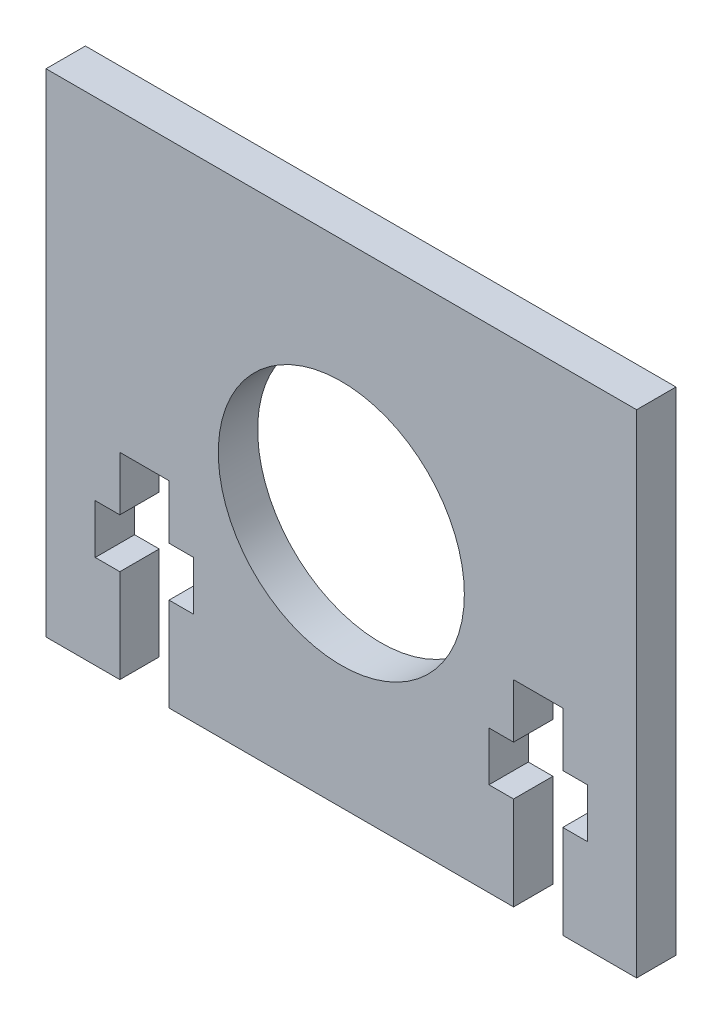
SolidWorks part; units mm, degrees
material "Pine"
ref_plane "Front Plane" through (0, 0, 0) normal (0, 0, 1) x (1, 0, 0)
ref_plane "Top Plane" through (0, 0, 0) normal (0, 1, 0) x (1, 0, 0)
ref_plane "Right Plane" through (0, 0, 0) normal (1, 0, 0) x (0, 0, -1)
sketch "Sketch1" plane through (0, 0, 0) normal (0, 0, 1) x (1, 0, 0)
  line L0 (0, -25) -> (0, 25) construction
  line L1 (30, 25) -> (-30, 25)
  line L2 (30, 25) -> (30, -25)
  line L3 (30, -25) -> (-30, -25)
  line L4 (-30, 25) -> (-30, -25)
  line L5 (30, 25) -> (-30, -25) construction
  line L6 (30, -25) -> (-30, 25) construction
  circle A0 centre (0, 0) radius 12.5
  point P0 (0, 0)
  dimension "D1" = 50
  dimension "D3" = 25
  dimension "D6" = 60
extrude "Boss-Extrude1" add sketch "Sketch1" along normal blind 4
sketch "Sketch2" plane through (0, 0, 4) normal (0, 0, 1) x (1, 0, 0)
  line L0 (-20, -25) -> (-20, 2.0451) construction
  line L1 (-30, -25) -> (30, -25) construction
  line L2 (20, -25) -> (20, 2.0451) construction
  line L3 (-30, 25) -> (-30, -25) construction
  line L4 (30, -25) -> (30, 25) construction
  line L5 (-30, -25) -> (30, -25) construction
  line L6 (-17.5, -5) -> (-22.5, -5)
  line L7 (-17.5, -5) -> (-17.5, -10.5)
  line L8 (-17.5, -25) -> (-22.5, -25)
  line L9 (-22.5, -5) -> (-22.5, -10.5)
  line L10 (-17.5, -5) -> (-22.5, -25) construction
  line L11 (-17.5, -25) -> (-22.5, -5) construction
  line L12 (22.5, -5) -> (17.5, -5)
  line L13 (22.5, -5) -> (22.5, -10.5)
  line L14 (22.5, -25) -> (17.5, -25)
  line L15 (17.5, -5) -> (17.5, -10.5)
  line L16 (22.5, -5) -> (17.5, -25) construction
  line L17 (22.5, -25) -> (17.5, -5) construction
  line L18 (-15, -10.5) -> (-17.5, -10.5)
  line L19 (-15, -10.5) -> (-15, -15.5)
  line L20 (-15, -15.5) -> (-17.5, -15.5)
  line L21 (-25, -10.5) -> (-25, -15.5)
  line L22 (-15, -10.5) -> (-25, -15.5) construction
  line L23 (-15, -15.5) -> (-25, -10.5) construction
  line L24 (25, -15.5) -> (22.5, -15.5)
  line L25 (25, -15.5) -> (25, -10.5)
  line L26 (25, -10.5) -> (22.5, -10.5)
  line L27 (15, -15.5) -> (15, -10.5)
  line L28 (25, -15.5) -> (15, -10.5) construction
  line L29 (25, -10.5) -> (15, -15.5) construction
  line L30 (-22.5, -10.5) -> (-25, -10.5)
  line L31 (-17.5, -15.5) -> (-17.5, -25)
  line L32 (-22.5, -15.5) -> (-25, -15.5)
  line L33 (-22.5, -15.5) -> (-22.5, -25)
  line L34 (17.5, -10.5) -> (15, -10.5)
  line L35 (17.5, -15.5) -> (17.5, -25)
  line L36 (17.5, -15.5) -> (15, -15.5)
  line L38 (22.5, -15.5) -> (22.5, -25)
  point P10 (-20, -15)
  point P15 (20, -15)
  point P20 (-20, -13)
  point P25 (20, -13)
  dimension "D1" = 10
  dimension "D2" = 10
  dimension "D3" = 20
  dimension "D4" = 5
  dimension "D5" = 5
  dimension "D6" = 10
  dimension "D7" = 12
  dimension "D8" = 12
  dimension "D9" = 20
extrude "Cut-Extrude1" cut sketch "Sketch2" against normal through all
